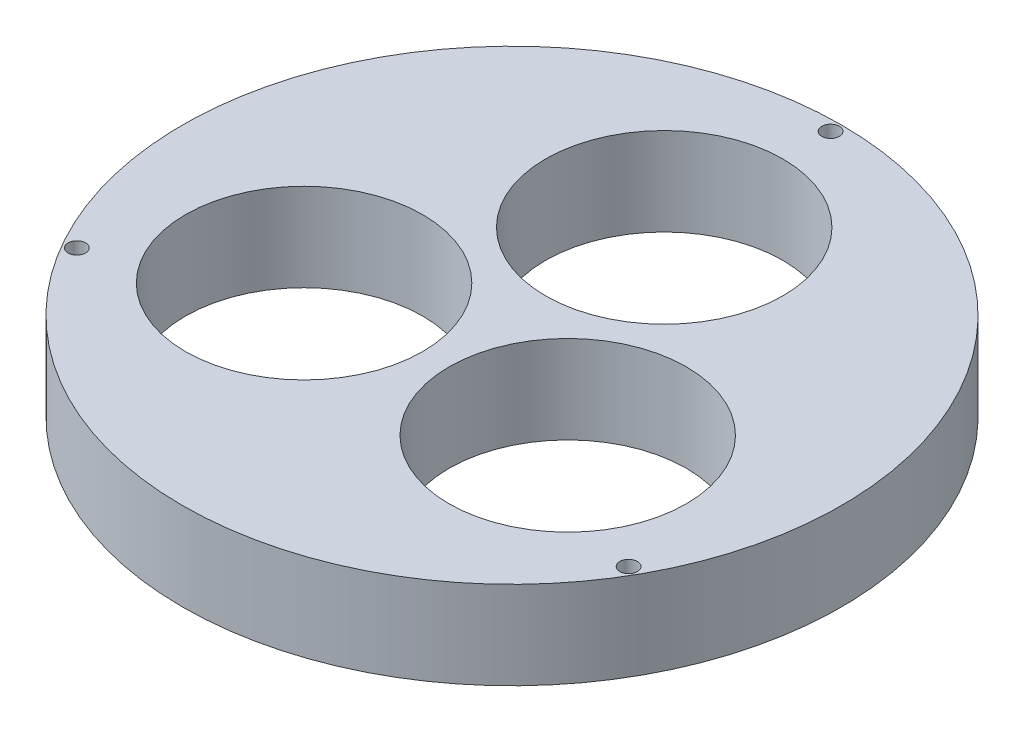
SolidWorks part; units mm, degrees
ref_plane "Front Plane" through (0, 0, 0) normal (0, 0, 1) x (1, 0, 0)
ref_plane "Top Plane" through (0, 0, 0) normal (0, 1, 0) x (1, 0, 0)
ref_plane "Right Plane" through (0, 0, 0) normal (1, 0, 0) x (0, 0, -1)
sketch "Sketch1" plane through (0, 0, 0) normal (0, 1, 0) x (1, 0, 0)
  line L0 (0, 0) -> (0, 37.5) construction
  line L1 (0, 0) -> (46.8525, -27.0503) construction
  line L2 (0, 0) -> (-49.1735, -28.3903) construction
  line L3 (0, 17.32) -> (14.9996, -8.66) construction
  circle A0 centre (0, 0) radius 37.5
  circle A1 centre (14.9996, -8.66) radius 13.5
  circle A2 centre (0, 17.32) radius 13.5
  circle A3 centre (-14.9996, -8.66) radius 13.5
  circle A4 centre (31.3934, -18.125) radius 1
  circle A5 centre (0, 36.25) radius 1
  circle A6 centre (-31.3934, -18.125) radius 1
  point P18 (0, 0)
  point P19 (0, 0)
  point P20 (0, 0)
  point P21 (0, 0)
  point P22 (0, 0)
  point P23 (0, 0)
  point P24 (0, 0)
  point P25 (0, 0)
  point P26 (0, 0)
  point P27 (0, 0)
  point P28 (0, 0)
  dimension "D1" = 17.32
  dimension "D2" = 17.32
  dimension "D3" = 17.32
  dimension "D4" = 36.25
  dimension "D5" = 36.25
  dimension "D6" = 36.25
extrude "Boss-Extrude3" add sketch "Sketch1" along normal blind 10
